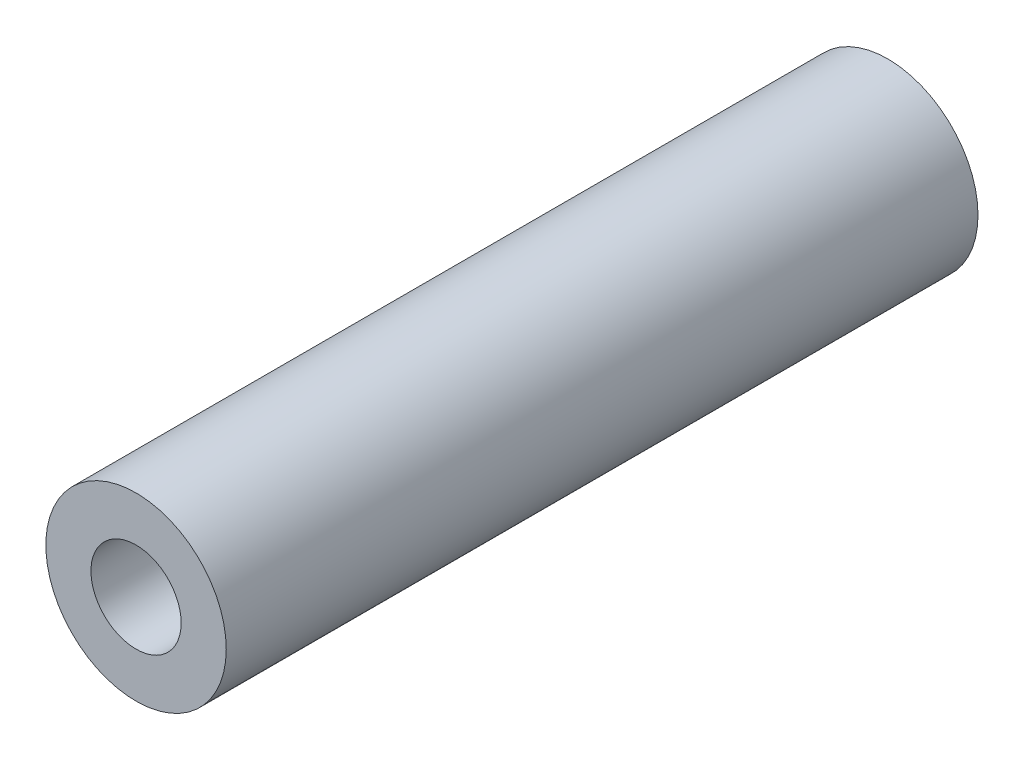
SolidWorks part; units mm, degrees
ref_plane "前视基准面" through (0, 0, 0) normal (0, 0, 1) x (1, 0, 0)
ref_plane "上视基准面" through (0, 0, 0) normal (0, 1, 0) x (1, 0, 0)
ref_plane "右视基准面" through (0, 0, 0) normal (1, 0, 0) x (0, 0, -1)
sketch "草图1" plane through (0, 0, 0) normal (0, 0, 1) x (1, 0, 0)
  circle A0 centre (0, 0) radius 3
  circle A1 centre (0, 0) radius 1.5
  dimension "D1" = 3
  dimension "D2" = 6
extrude "凸台-拉伸1" add sketch "草图1" along normal mid plane 25
